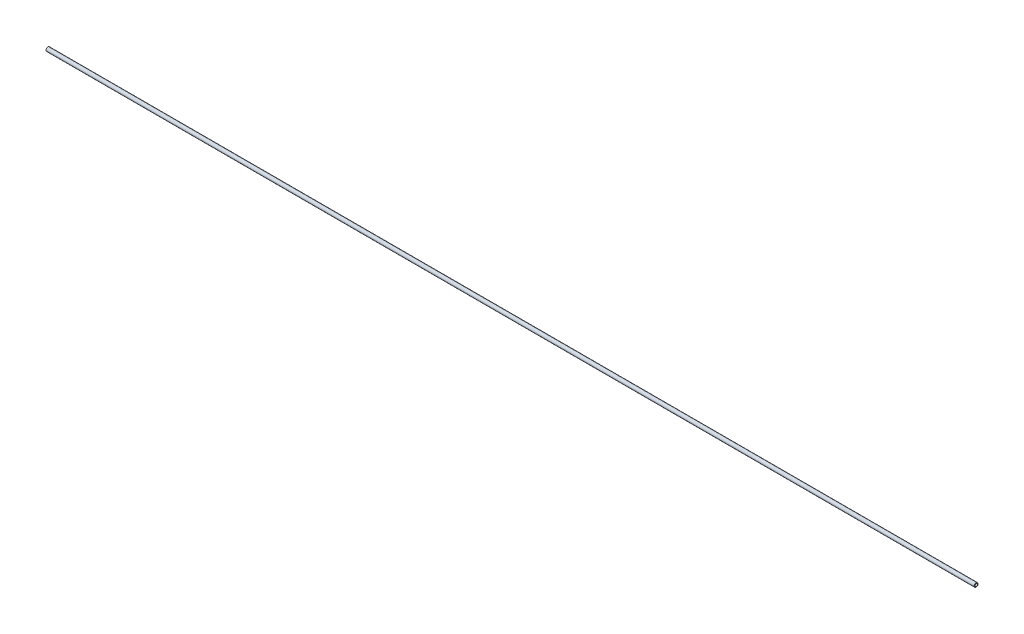
SolidWorks part; units mm, degrees
material "Alloy Steel"
ref_plane "Front Plane" through (0, 0, 0) normal (0, 0, 1) x (1, 0, 0)
ref_plane "Top Plane" through (0, 0, 0) normal (0, 1, 0) x (1, 0, 0)
ref_plane "Right Plane" through (0, 0, 0) normal (1, 0, 0) x (0, 0, -1)
ref_plane "Plane1" through (0, 0, 0) normal (-1, 0, 0) x (0, 0, 1)
sketch "Sketch1" plane through (0, 0, 0) normal (-1, 0, 0) x (0, 0, 1)
  circle A0 centre (0, 0) radius 3.175
  circle A1 centre (0, 0) radius 1.9304
  dimension "D1" = 6.35
  dimension "D2" = 3.8608
extrude "Extrude1" add sketch "Sketch1" along normal blind 1524
chamfer "Chamfer1" distance 0.381 angle 45 2 edges at (0, 0, 3.175) (-1524, 0, 3.175)
